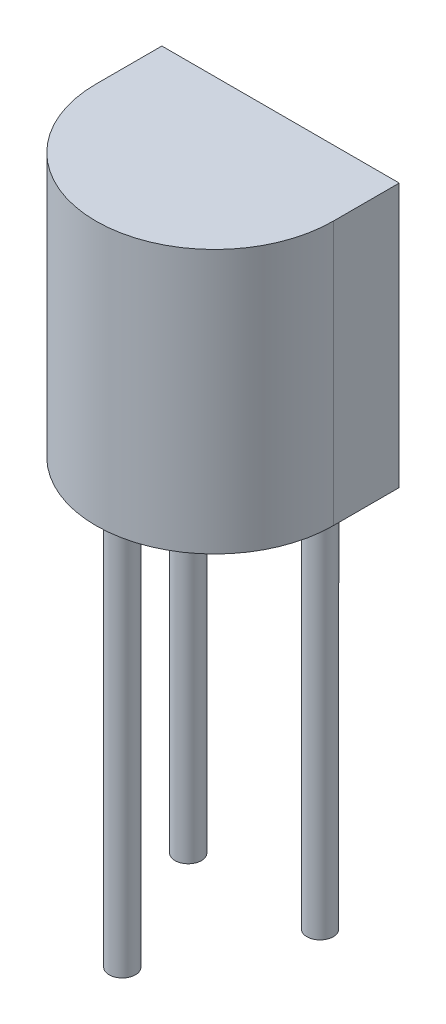
SolidWorks part; units mm, degrees
ref_plane "Front" through (0, 0, 0) normal (0, 0, 1) x (1, 0, 0)
ref_plane "Top" through (0, 0, 0) normal (0, 1, 0) x (1, 0, 0)
ref_plane "Right" through (0, 0, 0) normal (1, 0, 0) x (0, 0, -1)
sketch "Sketch1" plane through (0, 0, 0) normal (0, 1, 0) x (1, 0, 0)
  line L0 (0, 1.25) -> (4.5, 1.25)
  line L1 (4.5, 0) -> (4.5, 1.25)
  line L2 (0, 1.25) -> (0, 0)
  arc A1 (0, 0) -> (4.5, 0) centre (2.25, 0) ccw
  dimension "D1" = 1.25
  dimension "D2" = 4.5
extrude "Boss-Extrude1" add sketch "Sketch1" along normal blind 5
sketch "Sketch2" plane through (0, 0, 0) normal (0, -1, 0) x (1, 0, 0)
  line L0 (0, -1.25) -> (0, 0) construction
  line L1 (1, -0.75) -> (3.5, -0.75) construction
  line L3 (4.5, -1.25) -> (0, -1.25) construction
  circle A0 centre (1, -0.75) radius 0.25
  circle A1 centre (3.5, -0.75) radius 0.25
  circle A2 centre (2.25, 1.75) radius 0.25
  point P8 (2.25, -0.75)
  dimension "D1" = 0.5
  dimension "D2" = 0.5
  dimension "D3" = 0.5
  dimension "D5" = 0.5
  dimension "D4" = 2.5
  dimension "D6" = 1
  dimension "D7" = 2.5
extrude "Boss-Extrude2" add sketch "Sketch2" along normal blind 7.5
